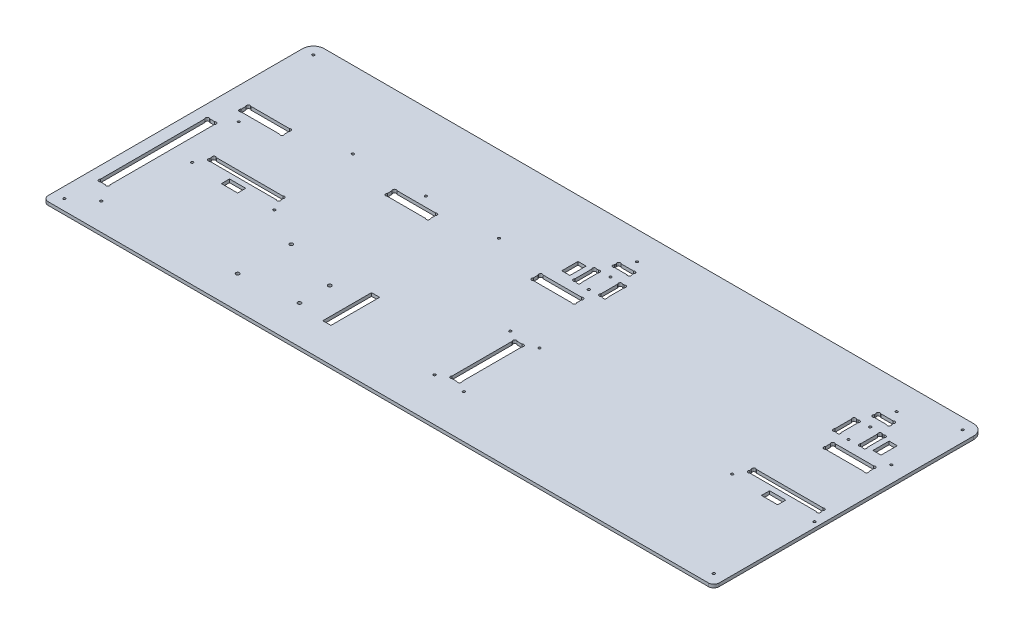
SolidWorks part; units mm, degrees
other "Marquage1"
sketch "Esquisse8" plane through (0, 3, 0) normal (-0.3047, 0.6733, 0.6737) x (0.9431, 0.1142, 0.3123)
ref_plane "Plan de face" through (0, 0, 0) normal (0, 0, 1) x (1, 0, 0)
ref_plane "Plan de dessus" through (0, 0, 0) normal (0, 1, 0) x (1, 0, 0)
ref_plane "Plan de droite" through (0, 0, 0) normal (1, 0, 0) x (0, 0, -1)
sketch "Esquisse1" plane through (0, 0, 0) normal (0, 1, 0) x (1, 0, 0)
  line L26 (317, 211.2627) -> (317, 212.7373)
  line L28 (319.2627, 215) -> (330.7373, 215)
  line L29 (333, 211.2627) -> (333, 212.7373)
  line L30 (330.7373, 209) -> (319.2627, 209)
  line L31 (312.2627, 179.5) -> (313.7373, 179.5)
  line L32 (312.2627, 199.5) -> (313.7373, 199.5)
  line L33 (310, 197.2373) -> (310, 181.7627)
  line L34 (316, 181.7627) -> (316, 197.2373)
  line L35 (334, 181.7627) -> (334, 197.2373)
  line L36 (340, 197.2373) -> (340, 181.7627)
  line L37 (337.7373, 199.5) -> (336.2627, 199.5)
  line L38 (337.7373, 179.5) -> (336.2627, 179.5)
  line L39 (552.2627, 179.5) -> (553.7373, 179.5)
  line L40 (552.2627, 199.5) -> (553.7373, 199.5)
  line L41 (550, 197.2373) -> (550, 181.7627)
  line L42 (556, 181.7627) -> (556, 197.2373)
  line L43 (574, 181.7627) -> (574, 197.2373)
  line L44 (580, 197.2373) -> (580, 181.7627)
  line L45 (577.7373, 199.5) -> (576.2627, 199.5)
  line L46 (577.7373, 179.5) -> (576.2627, 179.5)
  line L47 (559.2627, 209) -> (570.7373, 209)
  line L48 (557, 211.2627) -> (557, 212.7373)
  line L49 (570.7373, 215) -> (559.2627, 215)
  line L50 (573, 211.2627) -> (573, 212.7373)
  line L55 (560, 167.7373) -> (560, 163.2627)
  line L56 (600, 167.7373) -> (600, 163.2627)
  line L57 (562.2627, 170) -> (597.7373, 170)
  line L58 (597.7373, 161) -> (562.2627, 161)
  line L59 (292.2627, 161) -> (327.7373, 161)
  line L60 (327.7373, 170) -> (292.2627, 170)
  line L61 (290, 167.7373) -> (290, 163.2627)
  line L62 (330, 167.7373) -> (330, 163.2627)
  line L64 (20, 167.7373) -> (20, 163.2627)
  line L65 (60, 167.7373) -> (60, 163.2627)
  line L66 (22.2627, 170) -> (57.7373, 170)
  line L67 (57.7373, 161) -> (22.2627, 161)
  line L70 (155, 167.7373) -> (155, 163.2627)
  line L71 (195, 167.7373) -> (195, 163.2627)
  line L72 (157.2627, 170) -> (192.7373, 170)
  line L73 (192.7373, 161) -> (157.2627, 161)
  line L76 (10, 250) -> (610, 250)
  line L77 (0, 240) -> (0, 0)
  line L78 (0, 0) -> (620, 0)
  line L79 (620, 240) -> (620, 0)
  line L84 (13.2627, 40) -> (17.7373, 40)
  line L85 (13.2627, 141) -> (17.7373, 141)
  line L86 (11, 138.7373) -> (11, 42.2627)
  line L87 (20, 42.2627) -> (20, 138.7373)
  line L98 (337.7373, 45) -> (333.2627, 45)
  line L99 (337.7373, 105) -> (333.2627, 105)
  line L100 (340, 47.2627) -> (340, 102.7373)
  line L101 (331, 102.7373) -> (331, 47.2627)
  line L109 (610, 109.2627) -> (610, 110.7373)
  line L110 (544, 109.2627) -> (544, 110.7373)
  line L111 (607.7373, 107) -> (546.2627, 107)
  line L112 (546.2627, 113) -> (607.7373, 113)
  line L113 (108.7373, 113) -> (47.2627, 113)
  line L114 (47.2627, 107) -> (108.7373, 107)
  line L115 (111, 109.2627) -> (111, 110.7373)
  line L116 (45, 109.2627) -> (45, 110.7373)
  arc A0 (319.2627, 215) -> (317, 212.7373) centre (318.1314, 213.8686) ccw
  arc A1 (319.2627, 209) -> (317, 211.2627) centre (318.1314, 210.1314) cw
  arc A2 (330.7373, 209) -> (333, 211.2627) centre (331.8686, 210.1314) ccw
  arc A3 (330.7373, 215) -> (333, 212.7373) centre (331.8686, 213.8686) cw
  arc A4 (313.7373, 179.5) -> (316, 181.7627) centre (314.8686, 180.6314) ccw
  arc A5 (312.2627, 179.5) -> (310, 181.7627) centre (311.1314, 180.6314) cw
  arc A6 (312.2627, 199.5) -> (310, 197.2373) centre (311.1314, 198.3686) ccw
  arc A7 (313.7373, 199.5) -> (316, 197.2373) centre (314.8686, 198.3686) cw
  arc A8 (336.2627, 179.5) -> (334, 181.7627) centre (335.1314, 180.6314) cw
  arc A9 (336.2627, 199.5) -> (334, 197.2373) centre (335.1314, 198.3686) ccw
  arc A10 (337.7373, 199.5) -> (340, 197.2373) centre (338.8686, 198.3686) cw
  arc A11 (337.7373, 179.5) -> (340, 181.7627) centre (338.8686, 180.6314) ccw
  arc A12 (552.2627, 179.5) -> (550, 181.7627) centre (551.1314, 180.6314) cw
  arc A13 (552.2627, 199.5) -> (550, 197.2373) centre (551.1314, 198.3686) ccw
  arc A14 (553.7373, 199.5) -> (556, 197.2373) centre (554.8686, 198.3686) cw
  arc A15 (553.7373, 179.5) -> (556, 181.7627) centre (554.8686, 180.6314) ccw
  arc A16 (576.2627, 199.5) -> (574, 197.2373) centre (575.1314, 198.3686) ccw
  arc A17 (577.7373, 199.5) -> (580, 197.2373) centre (578.8686, 198.3686) cw
  arc A18 (577.7373, 179.5) -> (580, 181.7627) centre (578.8686, 180.6314) ccw
  arc A19 (576.2627, 179.5) -> (574, 181.7627) centre (575.1314, 180.6314) cw
  arc A20 (559.2627, 215) -> (557, 212.7373) centre (558.1314, 213.8686) ccw
  arc A21 (559.2627, 209) -> (557, 211.2627) centre (558.1314, 210.1314) cw
  arc A22 (570.7373, 209) -> (573, 211.2627) centre (571.8686, 210.1314) ccw
  arc A23 (570.7373, 215) -> (573, 212.7373) centre (571.8686, 213.8686) cw
  arc A29 (560, 163.2627) -> (562.2627, 161) centre (561.1314, 162.1314) ccw
  arc A30 (560, 167.7373) -> (562.2627, 170) centre (561.1314, 168.8686) cw
  arc A31 (600, 167.7373) -> (597.7373, 170) centre (598.8686, 168.8686) ccw
  arc A32 (600, 163.2627) -> (597.7373, 161) centre (598.8686, 162.1314) cw
  arc A34 (290, 163.2627) -> (292.2627, 161) centre (291.1314, 162.1314) ccw
  arc A35 (290, 167.7373) -> (292.2627, 170) centre (291.1314, 168.8686) cw
  arc A36 (330, 167.7373) -> (327.7373, 170) centre (328.8686, 168.8686) ccw
  arc A37 (330, 163.2627) -> (327.7373, 161) centre (328.8686, 162.1314) cw
  arc A40 (20, 163.2627) -> (22.2627, 161) centre (21.1314, 162.1314) ccw
  arc A41 (20, 167.7373) -> (22.2627, 170) centre (21.1314, 168.8686) cw
  arc A42 (60, 167.7373) -> (57.7373, 170) centre (58.8686, 168.8686) ccw
  arc A43 (60, 163.2627) -> (57.7373, 161) centre (58.8686, 162.1314) cw
  arc A44 (155, 163.2627) -> (157.2627, 161) centre (156.1314, 162.1314) ccw
  arc A45 (155, 167.7373) -> (157.2627, 170) centre (156.1314, 168.8686) cw
  arc A46 (195, 163.2627) -> (192.7373, 161) centre (193.8686, 162.1314) cw
  arc A47 (195, 167.7373) -> (192.7373, 170) centre (193.8686, 168.8686) ccw
  arc A50 (17.7373, 40) -> (20, 42.2627) centre (18.8686, 41.1314) ccw
  arc A52 (13.2627, 40) -> (11, 42.2627) centre (12.1314, 41.1314) cw
  arc A53 (17.7373, 141) -> (20, 138.7373) centre (18.8686, 139.8686) cw
  arc A54 (13.2627, 141) -> (11, 138.7373) centre (12.1314, 139.8686) ccw
  arc A56 (10, 250) -> (0, 240) centre (10, 240) ccw
  arc A57 (610, 250) -> (620, 240) centre (610, 240) cw
  arc A59 (331, 47.2627) -> (333.2627, 45) centre (332.1314, 46.1314) ccw
  arc A60 (340, 47.2627) -> (337.7373, 45) centre (338.8686, 46.1314) cw
  arc A61 (331, 102.7373) -> (333.2627, 105) centre (332.1314, 103.8686) cw
  arc A62 (340, 102.7373) -> (337.7373, 105) centre (338.8686, 103.8686) ccw
  arc A64 (607.7373, 107) -> (610, 109.2627) centre (608.8686, 108.1314) ccw
  circle A65 centre (539, 98) radius 1.1
  arc A66 (607.7373, 113) -> (610, 110.7373) centre (608.8686, 111.8686) cw
  circle A67 centre (615, 98) radius 1.1
  arc A68 (546.2627, 113) -> (544, 110.7373) centre (545.1314, 111.8686) ccw
  arc A69 (546.2627, 107) -> (544, 109.2627) centre (545.1314, 108.1314) cw
  arc A70 (108.7373, 107) -> (111, 109.2627) centre (109.8686, 108.1314) ccw
  arc A71 (108.7373, 113) -> (111, 110.7373) centre (109.8686, 111.8686) cw
  arc A73 (47.2627, 113) -> (45, 110.7373) centre (46.1314, 111.8686) ccw
  arc A75 (47.2627, 107) -> (45, 109.2627) centre (46.1314, 108.1314) cw
  point P1 (337, 199.5)
  point P7 (340, 189.5)
  dimension "D25" = 6
  dimension "D28" = 16
  dimension "D29" = 20
  dimension "D32" = 9.5
  dimension "D33" = 35
  dimension "D39" = 10
  dimension "D49" = 1.1314
  dimension "D57" = 6
  dimension "D55" = 10
  dimension "D62" = 5
  dimension "D63" = 1.6
  dimension "D64" = 9
  dimension "D65" = 1.1314
  dimension "D66" = 1.1314
  dimension "D67" = 620
  dimension "D9" = 2.2627
  dimension "D10" = 1.6
  dimension "D78" = 3.7373
  dimension "D14" = 1.6
  dimension "D36" = 1.6
  dimension "D61" = 1.6
  dimension "D95" = 1.6
  dimension "D107" = 1.6
  dimension "D118" = 1.6
  dimension "D119" = 1.6
  dimension "D128" = 6
  dimension "D141" = 1.6
  dimension "D58" = 2.2
  dimension "D2" = 250
  dimension "D8" = 20
  dimension "D13" = 40
  dimension "D16" = 1.1314
  dimension "D17" = 1.1314
  dimension "D19" = 2.2627
  dimension "D20" = 2.2627
  dimension "D21" = 80
  dimension "D22" = 9
  dimension "D23" = 1.1314
  dimension "D24" = 1.1314
  dimension "D26" = 6
  dimension "D27" = 6
  dimension "D30" = 40
  dimension "D31" = 18
  dimension "D37" = 1.1314
  dimension "D38" = 2.2627
  dimension "D40" = 1.1314
  dimension "D41" = 1.1314
  dimension "D42" = 1.1314
  dimension "D43" = 1.1314
  dimension "D45" = 1
  dimension "D46" = 1.1314
  dimension "D47" = 1.1314
  dimension "D48" = 1.1314
  dimension "D51" = 3.7373
  dimension "D52" = 66
  dimension "D53" = 10
  dimension "D54" = 66
  dimension "D56" = 107
  dimension "D59" = 1.1314
  dimension "D60" = 2.2627
  dimension "D68" = 60
  dimension "D70" = 6
  dimension "D72" = 1.1314
  dimension "D73" = 1.1314
  dimension "D74" = 63.7373
  dimension "D75" = 2.2627
  dimension "D76" = 2.2627
  dimension "D77" = 45
  dimension "D79" = 45
  dimension "D83" = 280
  dimension "D84" = 1.1314
  dimension "D85" = 1.1314
  dimension "D86" = 1.1314
  dimension "D87" = 1.1314
  dimension "D88" = 9
  dimension "D89" = 101
  dimension "D90" = 40
  dimension "D91" = 11
  dimension "D96" = 1.1314
  dimension "D97" = 1.1314
  dimension "D98" = 1.1314
  dimension "D100" = 1.1314
  dimension "D105" = 9
  dimension "D106" = 40
  dimension "D108" = 20
  dimension "D109" = 80
  dimension "D110" = 1.1314
  dimension "D111" = 1.1314
  dimension "D112" = 1.1314
  dimension "D113" = 1.1314
  dimension "D114" = 40
  dimension "D115" = 95
  dimension "D116" = 95
  dimension "D117" = 40
  dimension "D120" = 1.1314
  dimension "D121" = 1.1314
  dimension "D122" = 1.1314
  dimension "D123" = 1.1314
  dimension "D124" = 1.1314
  dimension "D125" = 1.1314
  dimension "D126" = 1.1314
  dimension "D127" = 1.1314
  dimension "D129" = 6
  dimension "D130" = 6
  dimension "D132" = 20
  dimension "D133" = 16
  dimension "D135" = 35
  dimension "D136" = 9.5
  dimension "D139" = 1
  dimension "D140" = 18
  dimension "D142" = 1.1314
  dimension "D143" = 1.1314
  dimension "D144" = 1.1314
  dimension "D145" = 1.1314
  dimension "D146" = 1.1314
  dimension "D147" = 1.1314
  dimension "D148" = 1.1314
  dimension "D149" = 1.1314
  dimension "D150" = 1.1314
  dimension "D151" = 1.1314
  dimension "D152" = 1.1314
  dimension "D153" = 1.1314
  dimension "D154" = 9
  dimension "D155" = 5
extrude "Extrusion1" add sketch "Esquisse1" along normal blind 3
sketch "Esquisse2" plane through (0, 3, 0) normal (0, 1, 0) x (-1, 0, 0)
  line L0 (-610, -250) -> (-10, -250) construction
  line L5 (-620, 21.4973) -> (-620, -261.3021) construction
  line L7 (-573, -142.8) -> (-72, -142.8)
  line L8 (-573, -142.8) -> (-573, -147)
  line L9 (-573, -147) -> (-72, -147)
  line L10 (-72, -142.8) -> (-72, -147)
  dimension "D1" = 47
  dimension "D2" = 4.2
  dimension "D3" = 501
  dimension "D4" = 103
extrude "Enlèv. mat.-Extru.1" [suppressed] cut sketch "Esquisse2" against normal through all
sketch "Esquisse3" plane through (0, 3, 0) normal (0, 1, 0) x (1, 0, 0)
  line L0 (574, 197.2373) -> (574, 181.7627) construction
  line L1 (556, 181.7627) -> (556, 197.2373) construction
  line L2 (559.2627, 209) -> (570.7373, 209) construction
  line L4 (576.2627, 179.5) -> (577.7373, 179.5) construction
  line L5 (577.7373, 199.5) -> (576.2627, 199.5) construction
  line L6 (334, 197.2373) -> (334, 181.7627) construction
  circle A0 centre (565, 179.5) radius 1.1
  circle A1 centre (565, 199.5) radius 1.1
  circle A2 centre (325, 179.5) radius 1.1
  circle A3 centre (325, 199.5) radius 1.1
  dimension "D1" = 2.2
  dimension "D2" = 9
  dimension "D3" = 9
  dimension "D4" = 20
  dimension "D5" = 9.5
  dimension "D6" = 0
  dimension "D7" = 0
  dimension "D8" = 9
extrude "Enlèv. mat.-Extru.2" cut sketch "Esquisse3" against normal through all
fillet "Congé1" radius 5 2 edges at (620, 1.5, 0) (0, 1.5, 0)
sketch "Esquisse4" plane through (0, 0, 0) normal (0, -1, 0) x (1, 0, 0)
  line L0 (0, -240) -> (0, -5) construction
  line L1 (5, 0) -> (615, 0) construction
  line L2 (610, -250) -> (10, -250) construction
  line L3 (620, -5) -> (620, -240) construction
  circle A0 centre (10, -10) radius 1.1
  circle A1 centre (610, -10) radius 1.1
  circle A2 centre (610, -240) radius 1.1
  circle A3 centre (10, -240) radius 1.1
  dimension "D1" = 2.2
  dimension "D2" = 10
  dimension "D3" = 10
  dimension "D4" = 10
  dimension "D5" = 10
  dimension "D6" = 10
  dimension "D7" = 10
  dimension "D8" = 10
  dimension "D9" = 10
extrude "Enlèv. mat.-Extru.3" cut sketch "Esquisse4" against normal through all
sketch "Esquisse5" plane through (0, 3, 0) normal (0, 1, 0) x (1, 0, 0)
  line L1 (0, 240) -> (0, 5) construction
  line L2 (5, 0) -> (615, 0) construction
  circle A0 centre (151.27, 78.26) radius 1.59
  circle A1 centre (150, 30) radius 1.59
  circle A2 centre (202.07, 63.02) radius 1.59
  circle A3 centre (202.07, 35.08) radius 1.59
  dimension "D1" = 3.18
  dimension "D7" = 30
  dimension "D2" = 48.26
  dimension "D3" = 27.94
  dimension "D4" = 52.07
  dimension "D5" = 5.08
  dimension "D6" = 150
  dimension "D8" = 1.27
extrude "Enlèv. mat.-Extru.4" cut sketch "Esquisse5" against normal through all
sketch "Esquisse6" plane through (0, 3, 0) normal (0, 1, 0) x (1, 0, 0)
  line L0 (544, 110.7373) -> (544, 109.2627) construction
  line L1 (569.5, 102) -> (584.5, 102)
  line L2 (569.5, 102) -> (569.5, 94.5)
  line L3 (569.5, 94.5) -> (584.5, 94.5)
  line L4 (584.5, 102) -> (584.5, 94.5)
  line L5 (610, 109.2627) -> (610, 110.7373) construction
  line L6 (546.2627, 107) -> (607.7373, 107) construction
  line L8 (585, 197) -> (592.5, 197)
  line L9 (585, 197) -> (585, 182)
  line L10 (585, 182) -> (592.5, 182)
  line L11 (592.5, 197) -> (592.5, 182)
  line L12 (305, 197) -> (297.5, 197)
  line L13 (305, 197) -> (305, 182)
  line L14 (305, 182) -> (297.5, 182)
  line L15 (297.5, 197) -> (297.5, 182)
  line L16 (577.7373, 199.5) -> (576.2627, 199.5) construction
  line L17 (576.2627, 179.5) -> (577.7373, 179.5) construction
  line L18 (580, 181.7627) -> (580, 197.2373) construction
  line L19 (310, 197.2373) -> (310, 181.7627) construction
  line L20 (313.7373, 199.5) -> (312.2627, 199.5) construction
  line L21 (45, 110.7373) -> (45, 109.2627) construction
  line L22 (227.07, 76.63) -> (234.57, 76.63)
  line L23 (227.07, 76.63) -> (227.07, 31.63)
  line L24 (227.07, 31.63) -> (234.57, 31.63)
  line L25 (234.57, 76.63) -> (234.57, 31.63)
  line L26 (70.5, 102) -> (85.5, 102)
  line L27 (70.5, 102) -> (70.5, 94.5)
  line L28 (70.5, 94.5) -> (85.5, 94.5)
  line L29 (85.5, 102) -> (85.5, 94.5)
  circle A0 centre (150, 30) radius 1.59 construction
  circle A1 centre (151.27, 78.26) radius 1.59 construction
  circle A2 centre (202.07, 63.02) radius 1.59 construction
  dimension "D1" = 15
  dimension "D2" = 7.5
  dimension "D3" = 25.5
  dimension "D4" = 25.5
  dimension "D5" = 5
  dimension "D6" = 7.5
  dimension "D7" = 15
  dimension "D8" = 15
  dimension "D9" = 7.5
  dimension "D10" = 2.5
  dimension "D11" = 2.5
  dimension "D12" = 5
  dimension "D13" = 5
  dimension "D14" = 2.5
  dimension "D15" = 7.5
  dimension "D16" = 45
  dimension "D17" = 1.63
  dimension "D18" = 1.63
  dimension "D19" = 25
  dimension "D20" = 15
  dimension "D21" = 25.5
extrude "Enlèv. mat.-Extru.5" cut sketch "Esquisse6" against normal through all
sketch "Esquisse7" plane through (0, 3, 0) normal (0, 1, 0) x (1, 0, 0)
  line L1 (5, 0) -> (615, 0) construction
  line L2 (331, 102.7373) -> (331, 47.2627) construction
  line L3 (340, 47.2627) -> (340, 102.7373) construction
  line L4 (570.7373, 215) -> (559.2627, 215) construction
  line L5 (330.7373, 215) -> (319.2627, 215) construction
  line L6 (597.7373, 170) -> (562.2627, 170) construction
  line L7 (192.7373, 170) -> (157.2627, 170) construction
  line L8 (0, 240) -> (0, 5) construction
  line L10 (47.2627, 107) -> (108.7373, 107) construction
  line L11 (45, 110.7373) -> (45, 109.2627) construction
  line L12 (111, 109.2627) -> (111, 110.7373) construction
  circle A0 centre (349, 110) radius 1.1
  circle A1 centre (349, 40) radius 1.1
  circle A2 centre (322, 110) radius 1.1
  circle A3 centre (322, 40) radius 1.1
  circle A4 centre (605, 179) radius 1.1
  circle A5 centre (565, 224) radius 1.1
  circle A6 centre (325, 224) radius 1.1
  circle A7 centre (175, 179) radius 1.1
  circle A8 centre (242.5, 179) radius 1.1
  circle A9 centre (107.5, 179) radius 1.1
  circle A10 centre (116, 98) radius 1.1
  circle A11 centre (40, 98) radius 1.1
  circle A12 centre (29, 152) radius 1.1
  circle A13 centre (29, 25) radius 1.1
  point P34 (325, 215)
  point P38 (565, 215)
  point P47 (175, 170)
  dimension "D1" = 2.2
  dimension "D2" = 40
  dimension "D3" = 9
  dimension "D4" = 9
  dimension "D5" = 70
  dimension "D6" = 9
  dimension "D7" = 40
  dimension "D8" = 9
  dimension "D9" = 9
  dimension "D10" = 67.5
  dimension "D11" = 67.5
  dimension "D12" = 127
  dimension "D13" = 25
  dimension "D14" = 29
  dimension "D15" = 9
  dimension "D16" = 5
  dimension "D17" = 5
extrude "Enlèv. mat.-Extru.6" cut sketch "Esquisse7" against normal through all
